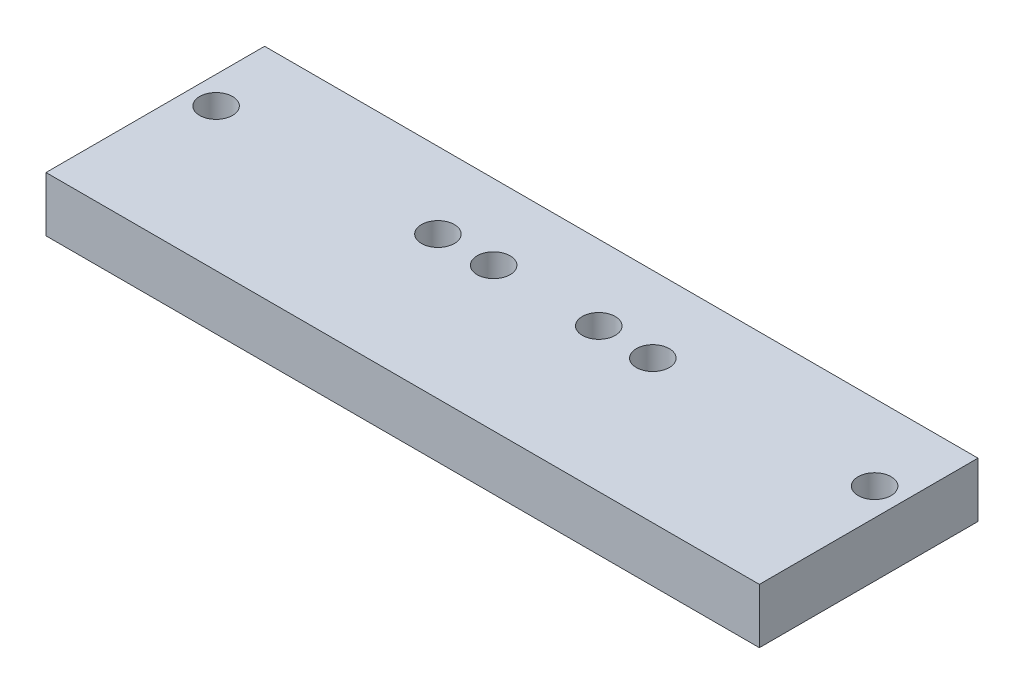
SolidWorks part; units mm, degrees
ref_plane "Front Plane" through (0, 0, 0) normal (0, 0, 1) x (1, 0, 0)
ref_plane "Top Plane" through (0, 0, 0) normal (0, 1, 0) x (1, 0, 0)
ref_plane "Right Plane" through (0, 0, 0) normal (1, 0, 0) x (0, 0, -1)
sketch "Sketch1" plane through (0, 0, 0) normal (0, 1, 0) x (1, 0, 0)
  line L1 (0, 0) -> (130, 0)
  line L2 (0, 0) -> (0, 39.84)
  line L3 (0, 39.84) -> (130, 39.84)
  line L4 (130, 0) -> (130, 39.84)
  dimension "D1" = 39.84
  dimension "D2" = 130
extrude "Boss-Extrude1" add sketch "Sketch1" along normal blind 10
sketch "Sketch2" plane through (0, 10, 0) normal (0, 1, 0) x (1, 0, 0)
  circle A0 centre (5, 25.9991) radius 3
  circle A1 centre (45.42, 25.9991) radius 3
  circle A2 centre (55.42, 26.1508) radius 3
  circle A3 centre (74.58, 26.1508) radius 3
  circle A4 centre (84.58, 25.9991) radius 3
  circle A5 centre (125, 25.9991) radius 3
extrude "Cut-Extrude1" cut sketch "Sketch2" against normal through all
